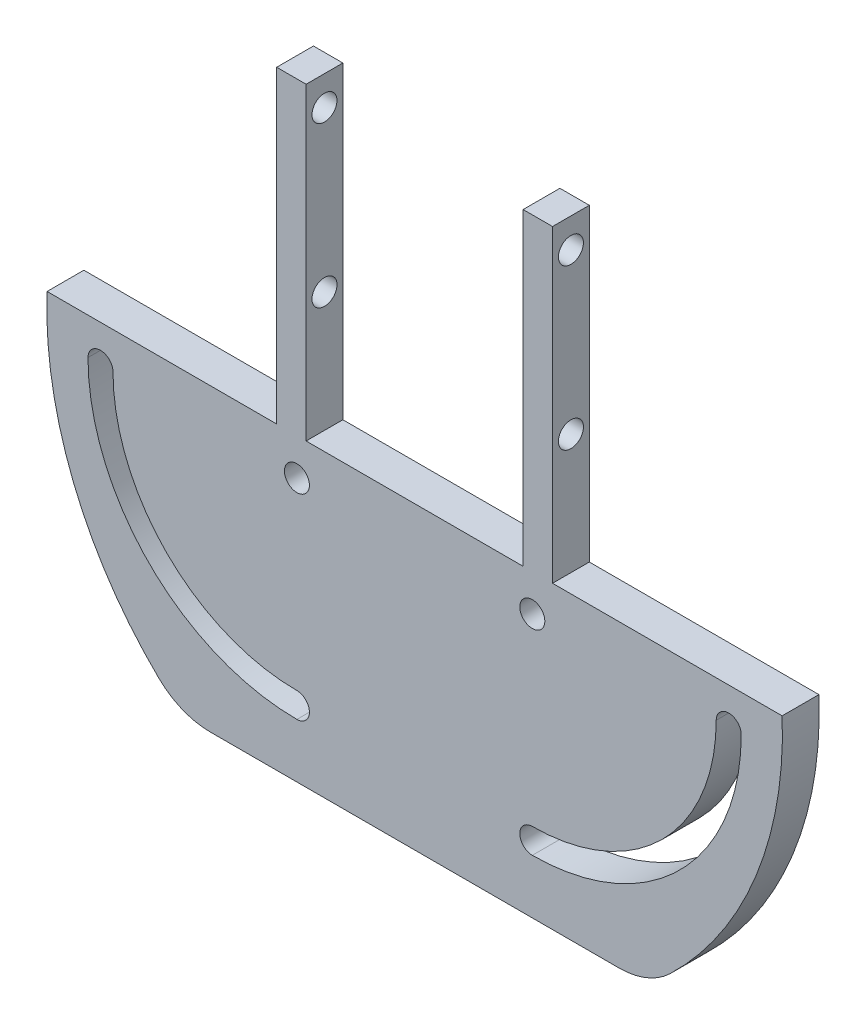
SolidWorks part; units mm, degrees
ref_plane "前视基准面" through (0, 0, 0) normal (0, 0, 1) x (1, 0, 0)
ref_plane "上视基准面" through (0, 0, 0) normal (0, 1, 0) x (1, 0, 0)
ref_plane "右视基准面" through (0, 0, 0) normal (1, 0, 0) x (0, 0, -1)
sketch "Sketch1" plane through (0, 0, 0) normal (0, 0, 1) x (1, 0, 0)
  line L0 (-49.96, 2) -> (49.96, 2)
  line L1 (0, 0) -> (0, -50) construction
  line L2 (-31.5688, -38.7739) -> (31.5688, -38.7739)
  arc A0 (49.96, 2) -> (31.5688, -38.7739) centre (0, 0) cw
  circle A1 centre (-16, -3) radius 1.7
  circle A2 centre (16, -3) radius 1.7
  arc A3 (-16, -29.7) -> (-42.7, -3) centre (-16, -3) cw construction
  arc A4 (-44.4, -3) -> (-16, -31.4) centre (-16, -3) ccw
  arc A5 (-41, -3) -> (-16, -28) centre (-16, -3) ccw
  arc A6 (-41, -3) -> (-44.4, -3) centre (-42.7, -3) ccw
  arc A7 (-16, -31.4) -> (-16, -28) centre (-16, -29.7) ccw
  arc A8 (16, -29.7) -> (42.7, -3) centre (16, -3) ccw construction
  arc A9 (16, -31.4) -> (44.4, -3) centre (16, -3) ccw
  arc A10 (16, -28) -> (41, -3) centre (16, -3) ccw
  arc A11 (16, -28) -> (16, -31.4) centre (16, -29.7) ccw
  arc A12 (44.4, -3) -> (41, -3) centre (42.7, -3) ccw
  arc A13 (-31.5688, -38.7739) -> (-49.96, 2) centre (0, 0) cw
  point P11 (-34.8798, -21.8798)
  point P18 (34.8798, -21.8798)
  dimension "D1" = 50
  dimension "D2" = 3.4
  dimension "D3" = 3.4
  dimension "D4" = 5
  dimension "D5" = 5
  dimension "D6" = 16
  dimension "D7" = 16
  dimension "D8" = 3.4
  dimension "D9" = 25
  dimension "D10" = 3.4
  dimension "D11" = 25
extrude "Boss-Extrude1" add sketch "Sketch1" against normal blind 5
sketch "Sketch2" plane through (0, 2, 0) normal (0, 1, 0) x (1, 0, 0)
  line L0 (0, 0) -> (0, 5) construction
  line L1 (49.96, 0) -> (-49.96, 0) construction
  line L2 (49.96, 5) -> (-49.96, 5) construction
  line L3 (18.75, 0) -> (18.75, 5)
  line L4 (-14.75, 0) -> (-18.75, 0)
  line L5 (-14.75, 0) -> (-14.75, 5)
  line L6 (-14.75, 5) -> (-18.75, 5)
  line L7 (-18.75, 0) -> (-18.75, 5)
  line L8 (14.75, 5) -> (18.75, 5)
  line L9 (14.75, 0) -> (14.75, 5)
  line L10 (14.75, 0) -> (18.75, 0)
  dimension "D1" = 14.75
  dimension "D2" = 18.75
extrude "Boss-Extrude2" add sketch "Sketch2" along normal blind 42
sketch "Sketch3" plane through (18.75, 0, 0) normal (1, 0, 0) x (0, 0, -1)
  line L0 (2.5, 44) -> (2.5, 2) construction
  line L1 (0, 44) -> (5, 44) construction
  line L2 (0, 2) -> (5, 2) construction
  circle A0 centre (2.5, 40) radius 1.7
  circle A1 centre (2.5, 18.3) radius 1.7
  dimension "D1" = 3.4
  dimension "D2" = 4
  dimension "D3" = 3.4
  dimension "D4" = 21.7
extrude "Cut-Extrude1" cut sketch "Sketch3" against normal through all
fillet "Fillet1" radius 10 1 edges at (31.5688, -38.7739, -2.5)
fillet "Fillet2" radius 10 1 edges at (-31.5688, -38.7739, -2.5)
